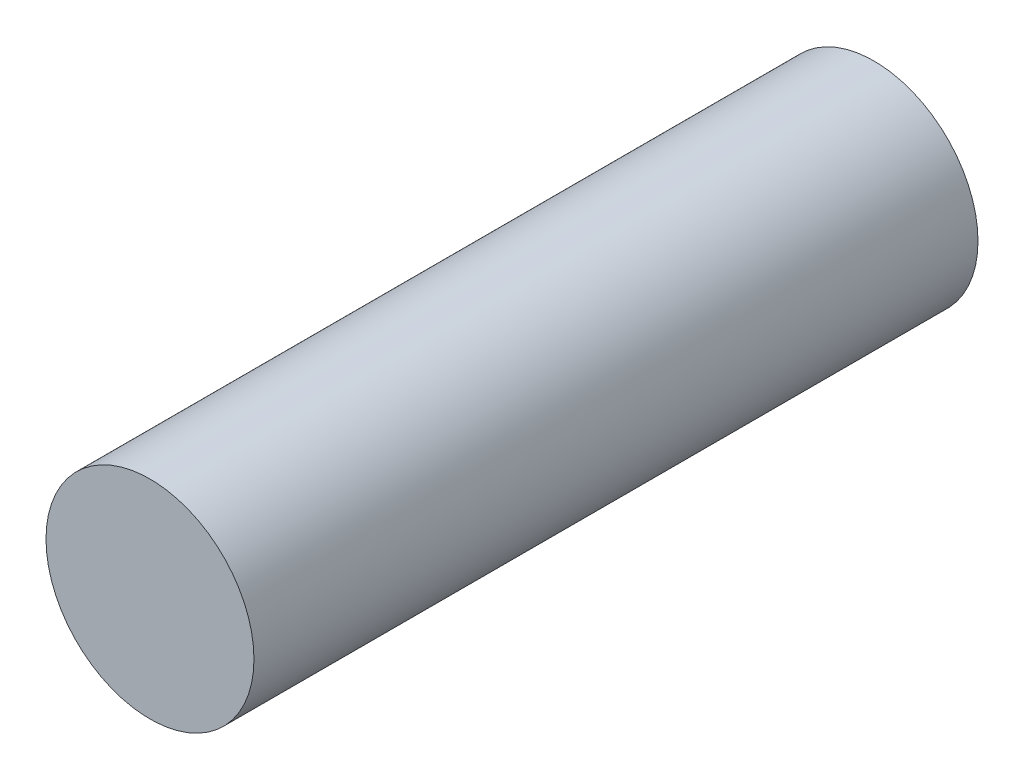
SolidWorks part; units mm, degrees
ref_plane "Front Plane" through (0, 0, 0) normal (0, 0, 1) x (1, 0, 0)
ref_plane "Top Plane" through (0, 0, 0) normal (0, 1, 0) x (1, 0, 0)
ref_plane "Right Plane" through (0, 0, 0) normal (1, 0, 0) x (0, 0, -1)
sketch "Sketch1" plane through (0, 0, 0) normal (0, 0, 1) x (1, 0, 0)
  circle A0 centre (0, 0) radius 7.2517
extrude "Boss-Extrude1" add sketch "Sketch1" along normal mid plane 50.4952
